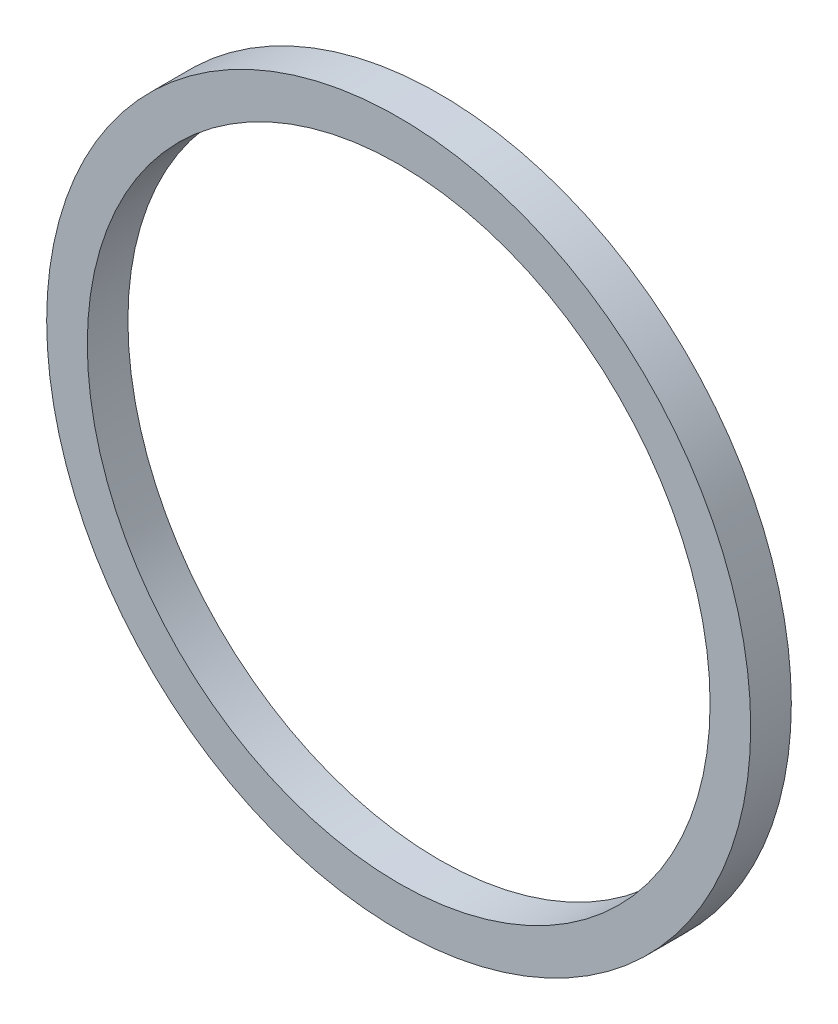
SolidWorks part; units mm, degrees
material "1060 Сплав"
ref_plane "Спереди" through (0, 0, 0) normal (0, 0, 1) x (1, 0, 0)
ref_plane "Сверху" through (0, 0, 0) normal (0, 1, 0) x (1, 0, 0)
ref_plane "Справа" through (0, 0, 0) normal (1, 0, 0) x (0, 0, -1)
sketch "Эскиз1" plane through (0, 0, 0) normal (0, 0, 1) x (1, 0, 0)
  circle A0 centre (0, 0) radius 13
  circle A1 centre (0, 0) radius 11.5
  dimension "D1" = 23
  dimension "D2" = 26
extrude "Бобышка-Вытянуть1" add sketch "Эскиз1" along normal blind 1.5
